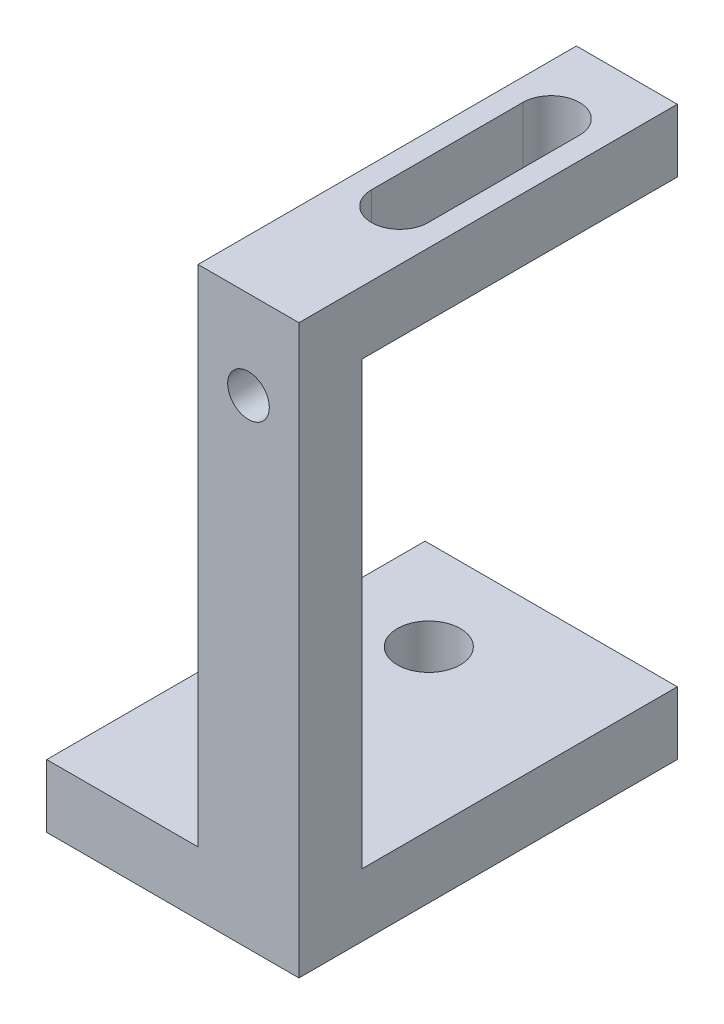
SolidWorks part; units mm, degrees
ref_plane "前视基准面" through (0, 0, 0) normal (0, 0, 1) x (1, 0, 0)
ref_plane "上视基准面" through (0, 0, 0) normal (0, 1, 0) x (1, 0, 0)
ref_plane "右视基准面" through (0, 0, 0) normal (1, 0, 0) x (0, 0, -1)
sketch "草图1" plane through (0, 0, 0) normal (0, 0, 1) x (1, 0, 0)
  line L1 (0, 0) -> (8, 0)
  line L2 (0, 0) -> (0, 20)
  line L3 (0, 20) -> (8, 20)
  line L4 (8, 0) -> (8, 20)
  dimension "D1" = 8
  dimension "D2" = 20
extrude "凸台-拉伸1" add sketch "草图1" along normal blind 10
sketch "草图2" plane through (0, 0, 0) normal (-1, 0, 0) x (0, 0, 1)
  line L0 (10, 0) -> (0, 0) construction
  line L1 (5, 0) -> (0, 0)
  line L2 (5, 0) -> (5, 15)
  line L3 (5, 15) -> (0, 15)
  line L4 (0, 0) -> (0, 15)
  line L5 (0, 20) -> (0, 0) construction
  line L6 (10, 20) -> (0, 20) construction
  line L7 (10, 20) -> (10, 0) construction
  point P8 (2.5, 15)
  dimension "D1" = 5
  dimension "D2" = 5
extrude "切除-拉伸1" cut sketch "草图2" against normal blind 10
sketch "草图3" plane through (0, 0, 0) normal (0, 0, -1) x (-1, 0, 0)
  line L0 (0, 20) -> (0, 15) construction
  line L1 (-8, 20) -> (0, 20)
  line L2 (-8, 20) -> (-8, 15)
  line L3 (-8, 15) -> (0, 15)
  line L4 (0, 20) -> (0, 15)
  line L5 (0, 15) -> (-8, 15) construction
extrude "凸台-拉伸2" add sketch "草图3" along normal blind 5
sketch "草图4" plane through (0, 0, 0) normal (0, -1, 0) x (1, 0, 0)
  line L1 (0, 5) -> (8, 5)
  line L2 (0, 5) -> (0, 10)
  line L3 (0, 10) -> (8, 10)
  line L4 (8, 5) -> (8, 10)
extrude "凸台-拉伸3" add sketch "草图4" along normal blind 20
sketch "草图5" plane through (0, -20, 0) normal (0, -1, 0) x (1, 0, 0)
  line L1 (8, 10) -> (-12, 10)
  line L2 (8, 10) -> (8, -20)
  line L3 (8, -20) -> (-12, -20)
  line L4 (-12, 10) -> (-12, -20)
  dimension "D1" = 30
  dimension "D2" = 20
extrude "凸台-拉伸4" add sketch "草图5" along normal blind 5
sketch "草图6" plane through (0, -20, 0) normal (0, 1, 0) x (1, 0, 0)
  circle A0 centre (-4.6, 12.8979) radius 2.5
extrude "切除-拉伸2" cut sketch "草图6" against normal blind 5
sketch "草图7" plane through (0, 0, -5) normal (0, 0, -1) x (-1, 0, 0)
  line L1 (-8, 20) -> (0, 20)
  line L2 (-8, 20) -> (-8, 15)
  line L3 (-8, 15) -> (0, 15)
  line L4 (0, 20) -> (0, 15)
extrude "凸台-拉伸5" add sketch "草图7" along normal blind 15
sketch "草图8" plane through (0, 20, 0) normal (0, 1, 0) x (1, 0, 0)
  line L0 (4, 20) -> (4, -12.9331) construction
  line L1 (0, 20) -> (8, 20) construction
  line L4 (6.25, 14) -> (6.25, 2)
  line L6 (1.75, 14) -> (1.75, 2)
  arc A0 (6.25, 14) -> (1.75, 14) centre (4, 14) ccw
  arc A1 (1.75, 2) -> (6.25, 2) centre (4, 2) ccw
  dimension "D1" = 4.5
  dimension "D2" = 4.5
  dimension "D3" = 6
  dimension "D4" = 12
extrude "切除-拉伸3" cut sketch "草图8" against normal blind 10
hole_wizard "M4 螺纹孔1" positions "草图9" profile "草图10" tap size "M4" standard "ISO"
sketch "草图9" plane through (0, 0, 10) normal (0, 0, 1) x (1, 0, 0)
  line L0 (4, 20) -> (4, 7.2033) construction
  line L1 (8, 20) -> (0, 20) construction
  point P0 (4, 13)
  dimension "D1" = 7
sketch "草图10" plane through (4, 13, 10) normal (1, 0, 0) x (0, -1, 0)
  line L0 (0, 0) -> (0, 11.0914)
  line L1 (0, 11.0914) -> (1.65, 10.1)
  line L2 (1.65, 10.1) -> (1.65, 0)
  line L5 (1.65, 0) -> (0, 0)
  line L10 (0, 11.0914) -> (-1.65, 10.1) construction
  line L11 (0, -6.35) -> (0, 107.95) construction
  dimension "螺纹孔钻头直径" = 3.3
  dimension "螺纹孔钻头深度" = 10.1
  dimension "导头角度" = 118
cosmetic thread "孔螺蚊线1" parameters "D1"=5, "D2"=4
